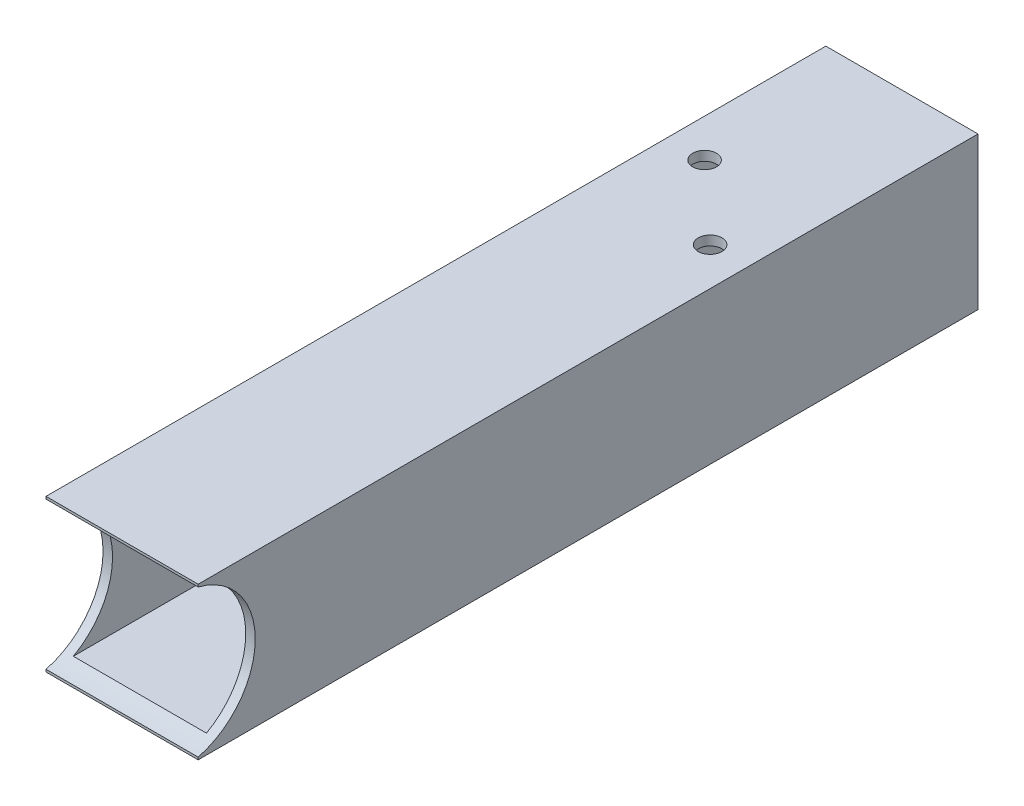
SolidWorks part; units mm, degrees
material "6061-T6 (SS)"
ref_plane "Front Plane" through (0, 0, 0) normal (0, 0, 1) x (1, 0, 0)
ref_plane "Top Plane" through (0, 0, 0) normal (0, 1, 0) x (1, 0, 0)
ref_plane "Right Plane" through (0, 0, 0) normal (1, 0, 0) x (0, 0, -1)
sketch "Sketch1" plane through (0, 0, 0) normal (0, 0, 1) x (1, 0, 0)
  line L0 (3.175, 47.625) -> (47.625, 47.625)
  line L1 (0, 0) -> (50.8, 0)
  line L2 (0, 0) -> (0, 50.8)
  line L3 (0, 50.8) -> (50.8, 50.8)
  line L4 (50.8, 0) -> (50.8, 50.8)
  line L5 (47.625, 3.175) -> (47.625, 47.625)
  line L6 (3.175, 3.175) -> (47.625, 3.175)
  line L7 (3.175, 3.175) -> (3.175, 47.625)
  dimension "D1" = 50.8
  dimension "D2" = 50.8
  dimension "D3" = 3.175
extrude "Boss-Extrude1" add sketch "Sketch1" along normal blind 260.35
sketch "Sketch2" plane through (50.8, 0, 0) normal (1, 0, 0) x (0, 0, -1)
  line L0 (-260.35, 0) -> (-260.35, 50.8) construction
  line L2 (-260.35, 0) -> (0, 0) construction
  circle A0 centre (-266.7, 25.4) radius 25.4
  dimension "D1" = 50.8
  dimension "D2" = 6.35
  dimension "D3" = 25.4
extrude "Cut-Extrude1" cut sketch "Sketch2" against normal through all
sketch "Sketch3" plane through (0, 0, 0) normal (0, -1, 0) x (1, 0, 0)
  line L18 (12.7, 57.1438) -> (12.7, 49.2063) construction
  circle A12 centre (38.1, 76.7358) radius 3.9687
  circle A13 centre (12.7, 53.175) radius 3.9688
  point P0 (38.1, 76.7358)
  point P1 (38.1, 76.7358)
  point P2 (12.7, 53.175)
  point P12 (12.7, 57.1438)
  point P22 (12.7, 49.2063)
  point P23 (38.1, 76.7358)
  point P24 (12.7, 53.175)
  point P25 (38.1, 76.7358)
extrude "Cut-Extrude2" cut sketch "Sketch3" against normal through all
